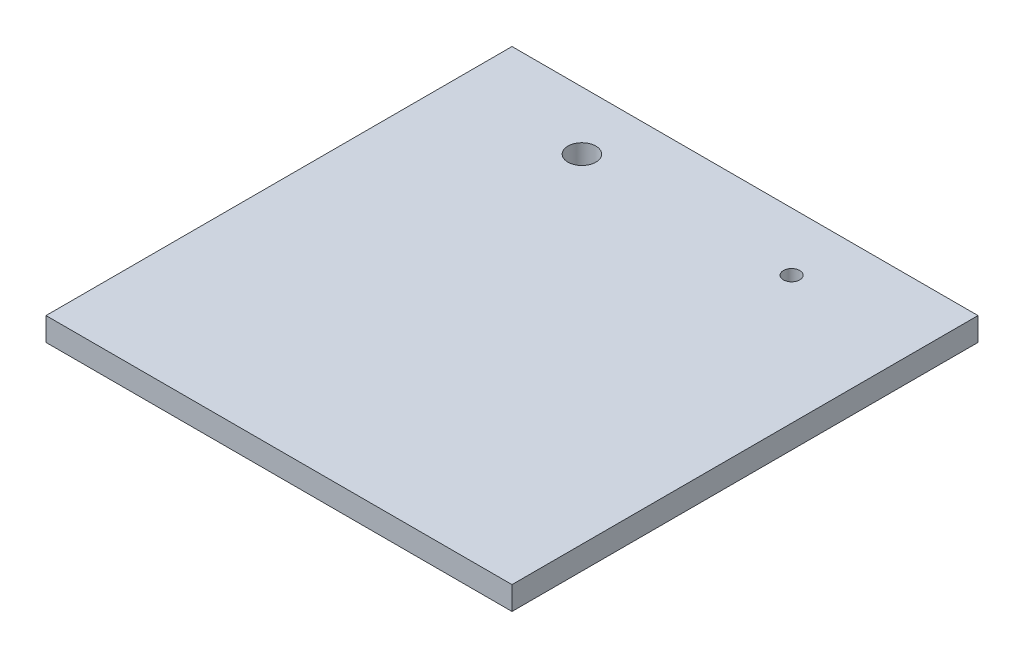
SolidWorks part; units mm, degrees
material "GE-223 Carbon Based Ablator"
ref_plane "Front Plane" through (0, 0, 0) normal (0, 0, 1) x (1, 0, 0)
ref_plane "Top Plane" through (0, 0, 0) normal (0, 1, 0) x (1, 0, 0)
ref_plane "Right Plane" through (0, 0, 0) normal (1, 0, 0) x (0, 0, -1)
sketch "Sketch1" plane through (0, 0, 0) normal (0, 1, 0) x (1, 0, 0)
  line L1 (-100, 100) -> (100, 100)
  line L2 (-100, 100) -> (-100, -100)
  line L3 (-100, -100) -> (100, -100)
  line L4 (100, 100) -> (100, -100)
  dimension "D1" = 200
  dimension "D2" = 200
  dimension "D3" = 100
  dimension "D4" = 100
extrude "Boss-Extrude1" add sketch "Sketch1" along normal blind 10
sketch "Sketch2" plane through (0, 10, 0) normal (0, 1, 0) x (1, 0, 0)
  line L0 (100, -100) -> (100, 100) construction
  line L1 (100, 100) -> (-100, 100) construction
  circle A0 centre (45, 75) radius 3.5
  dimension "D1" = 7
  dimension "D2" = 55
  dimension "D3" = 25
extrude "Cut-Extrude1" cut sketch "Sketch2" against normal through all contours A0
sketch "Sketch3" plane through (0, 10, 0) normal (0, 1, 0) x (1, 0, 0)
  line L0 (-100, 100) -> (-100, -100) construction
  line L2 (100, 100) -> (-100, 100) construction
  circle A0 centre (-45, 75) radius 6
  point P4 (0, 0)
  dimension "D1" = 12
  dimension "D2" = 55
  dimension "D3" = 25
extrude "Cut-Extrude2" cut sketch "Sketch3" against normal through all
